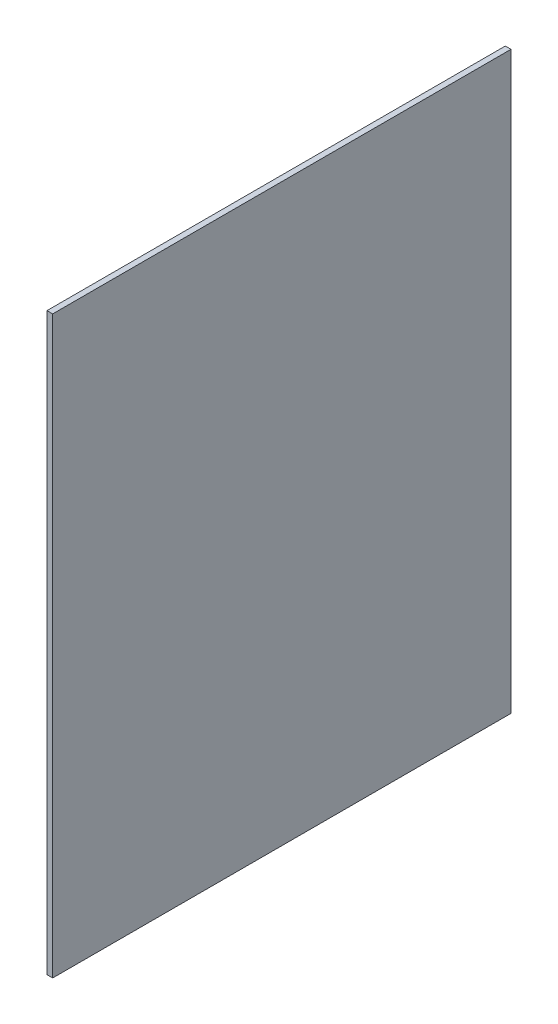
SolidWorks part; units mm, degrees
material "Plain Carbon Steel"
ref_plane "Front Plane" through (0, 0, 0) normal (0, 0, 1) x (1, 0, 0)
ref_plane "Top Plane" through (0, 0, 0) normal (0, 1, 0) x (1, 0, 0)
ref_plane "Right Plane" through (0, 0, 0) normal (1, 0, 0) x (0, 0, -1)
sketch "Sketch1" plane through (0, 0, 0) normal (0, 0, 1) x (1, 0, 0)
  line L0 (0, 0) -> (0, -150.8811) construction
  line L1 (0, -150.8811) -> (150.8811, -150.8811) construction
  line L2 (150.8811, -150.8811) -> (150.8811, 0) construction
  line L3 (150.8811, -140.8811) -> (150.8811, 0)
  line L4 (150.8811, 0) -> (152.2755, 0)
  line L5 (152.2755, 0) -> (152.2755, -140.8811)
  line L7 (150.8811, -140.8811) -> (152.2755, -140.8811)
  circle A0 centre (0, 0) radius 150.8811 construction
  dimension "D1" = 301.7622
  dimension "D2" = 1.3945
  dimension "D3" = 10
extrude "Boss-Extrude1" add sketch "Sketch1" along normal blind 112.268
